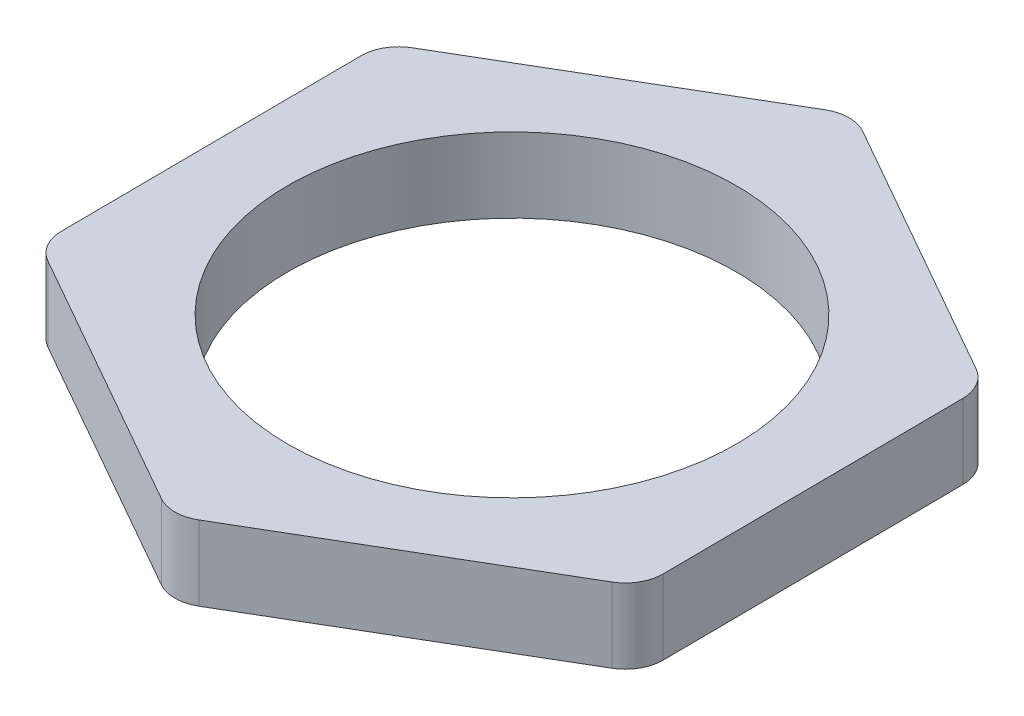
SolidWorks part; units mm, degrees
ref_plane "Front Plane" through (0, 0, 0) normal (0, 0, 1) x (1, 0, 0)
ref_plane "Top Plane" through (0, 0, 0) normal (0, 1, 0) x (1, 0, 0)
ref_plane "Right Plane" through (0, 0, 0) normal (1, 0, 0) x (0, 0, -1)
sketch "Sketch1" plane through (0, 0, 0) normal (0, 1, 0) x (1, 0, 0)
  line L1 (7.9663, 4.6766) -> (-0.0669, 9.2374)
  line L2 (-0.0669, 9.2374) -> (-8.0332, 4.5608)
  line L3 (-8.0332, 4.5608) -> (-7.9663, -4.6766)
  line L4 (-7.9663, -4.6766) -> (0.0669, -9.2374)
  line L5 (0.0669, -9.2374) -> (8.0332, -4.5608)
  line L6 (8.0332, -4.5608) -> (7.9663, 4.6766)
  circle A0 centre (0, 0) radius 6
  circle A1 centre (0, 0) radius 8 construction
  dimension "D1" = 12
  dimension "D2" = 8
extrude "Boss-Extrude1" add sketch "Sketch1" along normal blind 2
fillet "Fillet1" radius 1 6 edges at (-0.0669, 1, -9.2374) (7.9663, 1, -4.6766) (8.0332, 1, 4.5608) (0.0669, 1, 9.2374) (-7.9663, 1, 4.6766) (-8.0332, 1, -4.5608)
